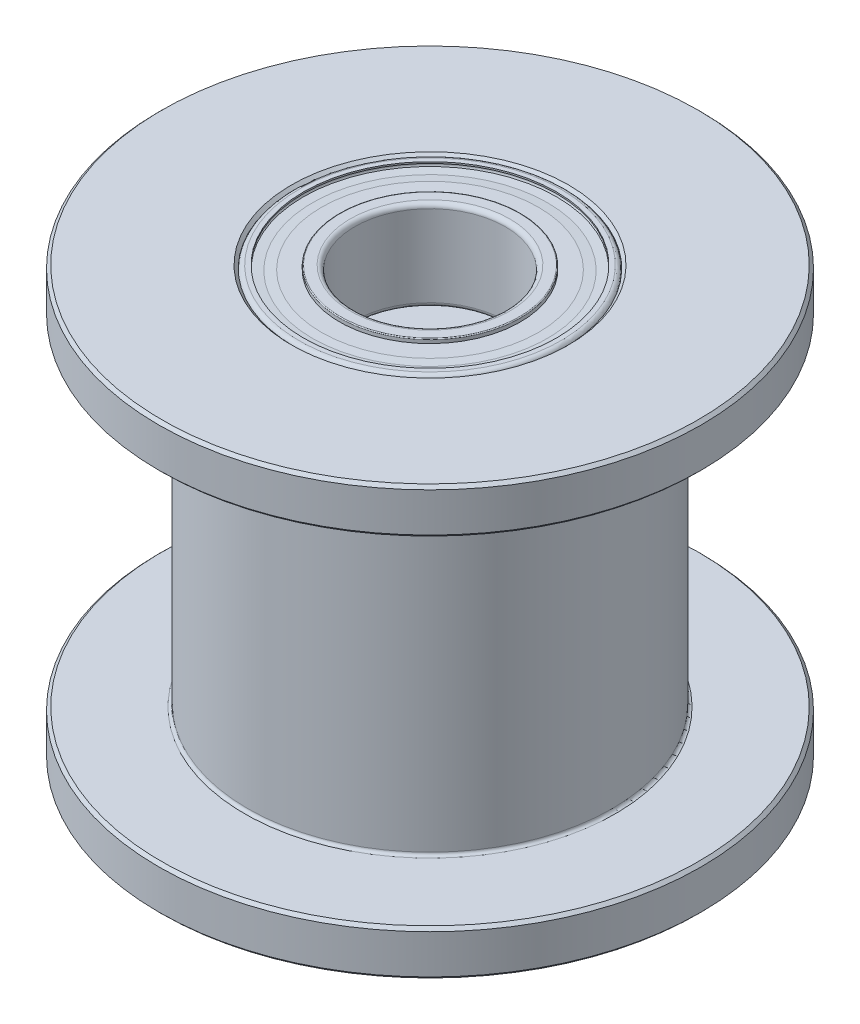
SolidWorks part; units mm, degrees
material "6061-T6 (SS)"
ref_plane "Přední rovina" through (0, 0, 0) normal (0, 0, 1) x (1, 0, 0)
ref_plane "Horní rovina" through (0, 0, 0) normal (0, 1, 0) x (1, 0, 0)
ref_plane "Pravá rovina" through (0, 0, 0) normal (1, 0, 0) x (0, 0, -1)
sketch "Skica1" plane through (0, 0, 0) normal (0, 0, 1) x (1, 0, 0)
  line L0 (4.5, 14.2) -> (9, 14.2)
  line L1 (9, 14.2) -> (9, 12.7)
  line L2 (9, 12.7) -> (6.05, 12.7)
  line L3 (6.05, 12.7) -> (6.05, 1.5)
  line L4 (6.05, 1.5) -> (9, 1.5)
  line L5 (9, 1.5) -> (9, 0)
  line L6 (9, 0) -> (4.5, 0)
  line L8 (4.5, 14.2) -> (4.5, 11.2)
  line L9 (4.5, 11.2) -> (1.5, 11.2)
  line L10 (1.5, 11.2) -> (1.5, 3)
  line L11 (1.5, 3) -> (4.5, 3)
  line L12 (4.5, 3) -> (4.5, 0)
  line L13 (0, 0) -> (0, -4.1646) construction
  dimension "D1" = 1.5
  dimension "D2" = 11.2
  dimension "D3" = 4.5
  dimension "D4" = 1.5
  dimension "D5" = 6.05
  dimension "D6" = 3
  dimension "D7" = 9
revolve "Rotovat1" add sketch "Skica1" angle 360 about L13
chamfer "Zkosení1" distance 0.1 angle 45 8 edges at (0, 3, 1.5) (0, 0, 4.5) (0, 11.2, 1.5) (0, 0, 9) (0, 1.5, 9) (0, 12.7, 9) (0, 14.2, 9) (0, 14.2, 4.5)
fillet "Zaoblit1" radius 0.1 4 edges at (0, 3, 4.5) (0, 1.5, 6.05) (0, 12.7, 6.05) (0, 11.2, 4.5)
sketch "Skica4" plane through (0, 0, 0) normal (0, 0, 1) x (1, 0, 0)
  line L0 (4.5, 14.05) -> (4.5, 11.35)
  line L1 (4.35, 11.2) -> (4.2, 11.2)
  line L2 (4.2, 11.2) -> (4.2, 11.25)
  line L3 (3.85, 11.4828) -> (4.2132, 11.429)
  line L4 (3.85, 11.4828) -> (3.85, 12.2528)
  line L5 (3.85, 13.1472) -> (3.85, 13.9172)
  line L6 (3.85, 13.9172) -> (4.2132, 13.971)
  line L7 (4.35, 14.2) -> (4.2, 14.2)
  line L8 (4.2, 14.2) -> (4.2, 14.15)
  line L9 (0, 0) -> (0, 18.4294) construction
  line L10 (4.4, 11.2) -> (-4.4, 11.2) construction
  arc A0 (4.35, 14.2) -> (4.5, 14.05) centre (4.35, 14.05) cw
  arc A1 (4.35, 11.2) -> (4.5, 11.35) centre (4.35, 11.35) ccw
  arc A2 (4.2, 14.15) -> (4.2132, 13.971) centre (4.2, 14.06) cw
  arc A3 (3.85, 13.1472) -> (3.85, 12.2528) centre (3.45, 12.7) cw
  arc A4 (4.2, 11.25) -> (4.2132, 11.429) centre (4.2, 11.34) ccw
  point P26 (4.5, 12.7)
  point P29 (4.275, 11.2)
  dimension "D3" = 0.09
  dimension "D6" = 0.15
  dimension "D7" = 0.6
  dimension "D1" = 4.5
  dimension "D2" = 3.85
  dimension "D4" = 0.05
  dimension "D5" = 0.15
  dimension "D8" = 0.77
  dimension "D9" = 3
  dimension "D10" = 1.05
revolve "Rotovat2" add sketch "Skica4" angle 360 about L9
sketch "Skica5" plane through (0, 0, 0) normal (0, 0, 1) x (1, 0, 0)
  line L0 (2.5, 14.05) -> (2.5, 11.35)
  line L1 (2.65, 14.2) -> (2.97, 14.2)
  line L2 (3, 14.17) -> (3, 14.06)
  line L3 (3, 14.06) -> (3.6, 14.06)
  line L4 (3.6, 14.06) -> (3.9, 14.04)
  line L5 (3.9, 14.04) -> (4.2, 14.06)
  line L6 (4.2, 14.06) -> (4.2, 14.01)
  line L7 (4.2, 14.01) -> (3.9, 13.97)
  line L8 (3.9, 13.97) -> (3.6, 13.97)
  line L9 (3.6, 13.97) -> (3, 14.01)
  line L10 (3, 14.01) -> (3, 13.0969)
  line L11 (2.65, 11.2) -> (2.97, 11.2)
  line L12 (0, 0) -> (0, 20.363) construction
  line L13 (3, 11.23) -> (3, 11.34)
  line L21 (3, 11.39) -> (3, 12.3031)
  line L22 (3, 11.34) -> (3.6, 11.34)
  line L23 (3.6, 11.34) -> (3.8962, 11.3917)
  line L24 (3.8962, 11.3917) -> (4.1924, 11.34)
  line L25 (4.1924, 11.34) -> (4.1924, 11.39)
  line L26 (4.1924, 11.39) -> (3.8975, 11.4581)
  line L27 (3.8975, 11.4581) -> (3.5975, 11.4581)
  line L28 (3.5975, 11.4581) -> (3, 11.39)
  line L29 (-4.2, 11.2) -> (4.2, 11.2) construction
  arc A0 (2.65, 11.2) -> (2.5, 11.35) centre (2.65, 11.35) cw
  arc A1 (2.65, 14.2) -> (2.5, 14.05) centre (2.65, 14.05) ccw
  arc A2 (3, 14.17) -> (2.97, 14.2) centre (2.97, 14.17) ccw
  arc A3 (3, 11.23) -> (2.97, 11.2) centre (2.97, 11.23) cw
  arc A4 (3, 13.0969) -> (3, 12.3031) centre (3.45, 12.7) ccw
  dimension "D3" = 0.15
  dimension "D4" = 0.11
  dimension "D5" = 0.03
  dimension "D7" = 0.6
  dimension "D1" = 2.5
  dimension "D2" = 3
  dimension "D6" = 0.6
  dimension "D8" = 0.95
  dimension "D9" = 3
  dimension "D10" = 1.2
  dimension "D11" = 0.3
  dimension "D12" = 0.05
  dimension "D13" = 0.9
  dimension "D14" = 0.6
  dimension "D15" = 0.09
  dimension "D16" = 0.05
  dimension "D17" = 0.05
revolve "Rotovat3" add sketch "Skica5" angle 360 about L12
sketch "Skica6" plane through (0, 0, 0) normal (0, 0, 1) x (1, 0, 0)
  line L0 (3.45, 13.3) -> (3.45, 12.1)
  line L4 (-4.2, 11.2) -> (4.2, 11.2) construction
  arc A0 (3.45, 13.3) -> (3.45, 12.1) centre (3.45, 12.7) cw
  dimension "D1" = 0.6
  dimension "D2" = 1.5
  dimension "D3" = 3.45
revolve "Rotovat4" add sketch "Skica6" angle 360 about L0
pattern_circular "Kruhové pole1" count 8 over 360 about axis through (0, 0, 0) along (0, 1, 0) of bodies 105
sketch "Skica7" plane through (0, 0, 0) normal (0, 0, 1) x (1, 0, 0)
  line L0 (4.5, 2.85) -> (4.5, 0.15)
  line L1 (4.35, 0) -> (4.2, 0)
  line L2 (4.2, 0) -> (4.2, 0.05)
  line L3 (3.85, 0.2828) -> (4.2132, 0.229)
  line L4 (3.85, 0.2828) -> (3.85, 1.0528)
  line L5 (3.85, 1.9472) -> (3.85, 2.7172)
  line L6 (3.85, 2.7172) -> (4.2132, 2.771)
  line L7 (4.35, 3) -> (4.2, 3)
  line L8 (4.2, 3) -> (4.2, 2.95)
  line L9 (0, 0) -> (0, 11.2374) construction
  arc A0 (4.35, 3) -> (4.5, 2.85) centre (4.35, 2.85) cw
  arc A1 (4.35, 0) -> (4.5, 0.15) centre (4.35, 0.15) ccw
  arc A2 (4.2, 2.95) -> (4.2132, 2.771) centre (4.2, 2.86) cw
  arc A3 (3.85, 1.9472) -> (3.85, 1.0528) centre (3.45, 1.5) cw
  arc A4 (4.2, 0.05) -> (4.2132, 0.229) centre (4.2, 0.14) ccw
  point P19 (4.5, 1.5)
  point P20 (4.275, 0)
  dimension "D1" = 0.09
  dimension "D4" = 0.15
  dimension "D5" = 0.6
  dimension "D2" = 0.05
  dimension "D3" = 0.15
  dimension "D6" = 0.77
  dimension "D7" = 3
  dimension "D8" = 1.05
  dimension "D9" = 4.5
  dimension "D10" = 3.85
revolve "Rotovat5" add sketch "Skica7" angle 360 about L9
sketch "Skica8" plane through (0, 0, 0) normal (0, 0, 1) x (1, 0, 0)
  line L0 (2.5, 2.85) -> (2.5, 0.15)
  line L1 (2.65, 3) -> (2.97, 3)
  line L2 (3, 2.97) -> (3, 2.86)
  line L3 (3, 2.86) -> (3.6, 2.86)
  line L4 (3.6, 2.86) -> (3.9, 2.84)
  line L5 (3.9, 2.84) -> (4.2, 2.86)
  line L6 (4.2, 2.86) -> (4.2, 2.81)
  line L7 (4.2, 2.81) -> (3.9, 2.77)
  line L8 (3.9, 2.77) -> (3.6, 2.77)
  line L9 (3.6, 2.77) -> (3, 2.81)
  line L10 (3, 2.81) -> (3, 1.8969)
  line L11 (2.65, 0) -> (2.97, 0)
  line L12 (3, 0.03) -> (3, 0.14)
  line L13 (3, 0.19) -> (3, 1.1031)
  line L14 (3, 0.14) -> (3.6, 0.14)
  line L15 (3.6, 0.14) -> (3.8962, 0.1917)
  line L16 (3.8962, 0.1917) -> (4.1924, 0.14)
  line L17 (4.1924, 0.14) -> (4.1924, 0.19)
  line L18 (4.1924, 0.19) -> (3.8975, 0.2581)
  line L19 (3.8975, 0.2581) -> (3.5975, 0.2581)
  line L20 (3.5975, 0.2581) -> (3, 0.19)
  line L21 (0, 0) -> (0, -2.9362) construction
  arc A0 (2.65, 0) -> (2.5, 0.15) centre (2.65, 0.15) cw
  arc A1 (2.65, 3) -> (2.5, 2.85) centre (2.65, 2.85) ccw
  arc A2 (3, 2.97) -> (2.97, 3) centre (2.97, 2.97) ccw
  arc A3 (3, 0.03) -> (2.97, 0) centre (2.97, 0.03) cw
  arc A4 (3, 1.8969) -> (3, 1.1031) centre (3.45, 1.5) ccw
  dimension "D1" = 0.15
  dimension "D2" = 0.03
  dimension "D5" = 0.6
  dimension "D3" = 0.11
  dimension "D4" = 0.6
  dimension "D6" = 0.95
  dimension "D7" = 3
  dimension "D8" = 1.2
  dimension "D9" = 0.3
  dimension "D10" = 0.05
  dimension "D11" = 0.9
  dimension "D12" = 0.6
  dimension "D13" = 0.09
  dimension "D14" = 0.05
  dimension "D15" = 0.05
  dimension "D16" = 2.5
  dimension "D17" = 3
revolve "Rotovat6" add sketch "Skica8" angle 360 about L21
sketch "Skica9" plane through (0, 0, 0) normal (0, 0, 1) x (1, 0, 0)
  line L0 (3.45, 2.1) -> (3.45, 0.9)
  line L1 (0, -2.351) -> (0, 5.6956) construction
  arc A0 (3.45, 2.1) -> (3.45, 0.9) centre (3.45, 1.5) cw
  dimension "D1" = 0.6
  dimension "D2" = 3.45
  dimension "D3" = 1.5
revolve "Rotovat7" add sketch "Skica9" angle 360 about L0
pattern_circular "Kruhové pole3" count 8 over 360 about axis through (0, 0, 0) along (0, 1, 0) of bodies 123
